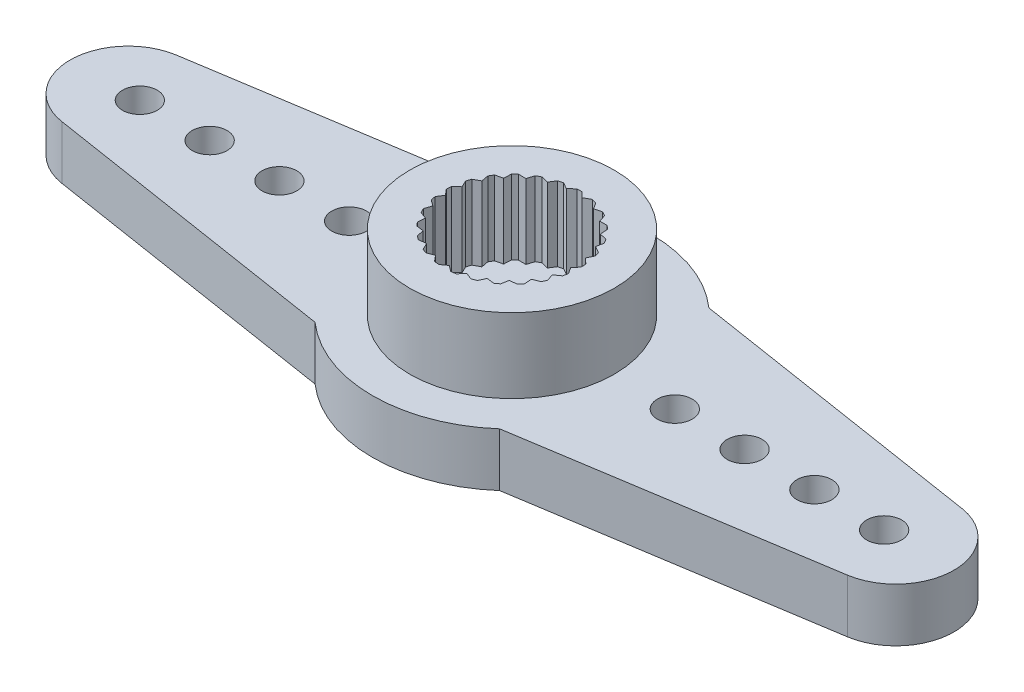
SolidWorks part; units mm, degrees
material "ABS"
ref_plane "Front Plane" through (0, 0, 0) normal (0, 0, 1) x (1, 0, 0)
ref_plane "Top Plane" through (0, 0, 0) normal (0, 1, 0) x (1, 0, 0)
ref_plane "Right Plane" through (0, 0, 0) normal (1, 0, 0) x (0, 0, -1)
sketch "Sketch2" plane through (0, 0, 0) normal (0, 1, 0) x (1, 0, 0)
  circle A0 centre (0, 0) radius 6
  circle A1 centre (0, 0) radius 1.5
  dimension "D1" = 12
  dimension "D2" = 3
extrude "Boss-Extrude1" add sketch "Sketch2" along normal mid plane 2.3
sketch "Sketch3" plane through (0, 1.15, 0) normal (0, 1, 0) x (1, 0, 0)
  line L0 (0, 0) -> (0, 2.9) construction
  line L3 (0, 0) -> (0.376, 2.9763) construction
  line L52 (0.1074, 2.898) -> (0.3384, 2.6787)
  line L53 (-0.1074, 2.898) -> (-0.3384, 2.6787)
  line L54 (0.8248, 2.7802) -> (0.9939, 2.5104)
  line L55 (0.6167, 2.8337) -> (0.3384, 2.6787)
  line L56 (1.4903, 2.4878) -> (1.587, 2.1843)
  line L57 (1.302, 2.5913) -> (0.9939, 2.5104)
  line L58 (2.0621, 2.039) -> (2.0804, 1.721)
  line L59 (1.9055, 2.1861) -> (1.587, 2.1843)
  line L60 (2.5044, 1.4621) -> (2.443, 1.1496)
  line L61 (2.3893, 1.6435) -> (2.0804, 1.721)
  line L62 (2.7894, 0.7934) -> (2.6522, 0.5059)
  line L63 (2.723, 0.9977) -> (2.443, 1.1496)
  line L64 (2.899, 0.0748) -> (2.6947, -0.1695)
  line L65 (2.8855, 0.2892) -> (2.6522, 0.5059)
  line L66 (2.8265, -0.6486) -> (2.5679, -0.8343)
  line L67 (2.8668, -0.4375) -> (2.6947, -0.1695)
  line L68 (2.5765, -1.3311) -> (2.2797, -1.4467)
  line L69 (2.6679, -1.1367) -> (2.5679, -0.8343)
  line L70 (2.1645, -1.93) -> (1.8483, -1.9682)
  line L71 (2.3014, -1.7645) -> (2.2797, -1.4467)
  line L72 (1.6165, -2.4077) -> (1.3007, -2.366)
  line L73 (1.7903, -2.2814) -> (1.8483, -1.9682)
  line L74 (0.967, -2.734) -> (0.6715, -2.6152)
  line L75 (1.1667, -2.655) -> (1.3007, -2.366)
  line L76 (0.2566, -2.8886) -> (0, -2.7)
  line L77 (0.4698, -2.8617) -> (0.6715, -2.6152)
  line L78 (-0.4698, -2.8617) -> (-0.6715, -2.6152)
  line L79 (-0.2566, -2.8886) -> (0, -2.7)
  line L80 (-1.1667, -2.655) -> (-1.3007, -2.366)
  line L81 (-0.967, -2.734) -> (-0.6715, -2.6152)
  line L82 (-1.7903, -2.2814) -> (-1.8483, -1.9682)
  line L83 (-1.6165, -2.4077) -> (-1.3007, -2.366)
  line L84 (-2.3014, -1.7645) -> (-2.2797, -1.4467)
  line L85 (-2.1645, -1.93) -> (-1.8483, -1.9682)
  line L86 (-2.6679, -1.1367) -> (-2.5679, -0.8343)
  line L87 (-2.5765, -1.3311) -> (-2.2797, -1.4467)
  line L88 (-2.8668, -0.4375) -> (-2.6947, -0.1695)
  line L89 (-2.8265, -0.6486) -> (-2.5679, -0.8343)
  line L90 (-2.8855, 0.2892) -> (-2.6522, 0.5059)
  line L91 (-2.899, 0.0748) -> (-2.6947, -0.1695)
  line L92 (-2.723, 0.9977) -> (-2.443, 1.1496)
  line L93 (-2.7894, 0.7934) -> (-2.6522, 0.5059)
  line L94 (-2.3893, 1.6435) -> (-2.0804, 1.721)
  line L95 (-2.5044, 1.4621) -> (-2.443, 1.1496)
  line L96 (-1.9055, 2.1861) -> (-1.587, 2.1843)
  line L97 (-2.0621, 2.039) -> (-2.0804, 1.721)
  line L98 (-1.302, 2.5913) -> (-0.9939, 2.5104)
  line L99 (-1.4903, 2.4878) -> (-1.587, 2.1843)
  line L100 (-0.6167, 2.8337) -> (-0.3384, 2.6787)
  line L101 (-0.8248, 2.7802) -> (-0.9939, 2.5104)
  line L102 (-2.533, 1.6075) -> (-2.3893, 1.6435) construction
  line L103 (-2.533, 1.6075) -> (-2.5044, 1.4621) construction
  line L104 (-2.8532, 0.9271) -> (-2.723, 0.9977) construction
  line L105 (-2.8532, 0.9271) -> (-2.7894, 0.7934) construction
  line L106 (-2.9941, 0.1884) -> (-2.8855, 0.2892) construction
  line L107 (-2.9941, 0.1884) -> (-2.899, 0.0748) construction
  line L108 (-2.9469, -0.5621) -> (-2.8668, -0.4375) construction
  line L109 (-2.9469, -0.5621) -> (-2.8265, -0.6486) construction
  line L110 (0, 3) -> (0.1074, 2.898) construction
  line L111 (0, 2.9) -> (0, 3) construction
  line L112 (0, 3) -> (-0.1074, 2.898) construction
  line L113 (-0.7461, 2.9057) -> (-0.6167, 2.8337) construction
  line L114 (-0.7461, 2.9057) -> (-0.8248, 2.7802) construction
  line L115 (-1.4453, 2.6289) -> (-1.302, 2.5913) construction
  line L116 (-1.4453, 2.6289) -> (-1.4903, 2.4878) construction
  line L117 (-2.0536, 2.1869) -> (-1.9055, 2.1861) construction
  line L118 (-2.0536, 2.1869) -> (-2.0621, 2.039) construction
  line L119 (-2.7145, -1.2773) -> (-2.6679, -1.1367) construction
  line L120 (-2.7145, -1.2773) -> (-2.5765, -1.3311) construction
  line L121 (-2.3115, -1.9123) -> (-2.3014, -1.7645) construction
  line L122 (-2.3115, -1.9123) -> (-2.1645, -1.93) construction
  line L123 (-1.7634, -2.4271) -> (-1.7903, -2.2814) construction
  line L124 (-1.7634, -2.4271) -> (-1.6165, -2.4077) construction
  line L125 (-1.1044, -2.7893) -> (-1.1667, -2.655) construction
  line L126 (-1.1044, -2.7893) -> (-0.967, -2.734) construction
  line L127 (-0.376, -2.9763) -> (-0.4698, -2.8617) construction
  line L128 (-0.376, -2.9763) -> (-0.2566, -2.8886) construction
  line L129 (0.376, -2.9763) -> (0.2566, -2.8886) construction
  line L130 (0.376, -2.9763) -> (0.4698, -2.8617) construction
  line L131 (1.1044, -2.7893) -> (0.967, -2.734) construction
  line L132 (1.1044, -2.7893) -> (1.1667, -2.655) construction
  line L133 (1.7634, -2.4271) -> (1.6165, -2.4077) construction
  line L134 (1.7634, -2.4271) -> (1.7903, -2.2814) construction
  line L135 (2.3115, -1.9123) -> (2.3014, -1.7645) construction
  line L136 (2.3115, -1.9123) -> (2.1645, -1.93) construction
  line L137 (2.7145, -1.2773) -> (2.6679, -1.1367) construction
  line L138 (2.7145, -1.2773) -> (2.5765, -1.3311) construction
  line L139 (2.9469, -0.5621) -> (2.8668, -0.4375) construction
  line L140 (2.9469, -0.5621) -> (2.8265, -0.6486) construction
  line L141 (2.9941, 0.1884) -> (2.8855, 0.2892) construction
  line L142 (2.9941, 0.1884) -> (2.899, 0.0748) construction
  line L143 (2.8532, 0.9271) -> (2.723, 0.9977) construction
  line L144 (2.8532, 0.9271) -> (2.7894, 0.7934) construction
  line L145 (2.533, 1.6075) -> (2.3893, 1.6435) construction
  line L146 (2.533, 1.6075) -> (2.5044, 1.4621) construction
  line L147 (2.0536, 2.1869) -> (1.9055, 2.1861) construction
  line L148 (2.0536, 2.1869) -> (2.0621, 2.039) construction
  line L149 (1.4453, 2.6289) -> (1.302, 2.5913) construction
  line L150 (1.4453, 2.6289) -> (1.4903, 2.4878) construction
  line L151 (0.7461, 2.9057) -> (0.6167, 2.8337) construction
  line L152 (0.7461, 2.9057) -> (0.8248, 2.7802) construction
  circle A0 centre (0, 0) radius 4.4
  circle A1 centre (0, 0) radius 3 construction
  circle A2 centre (0, 0) radius 2.7 construction
  arc A3 (-0.6167, 2.8337) -> (-0.8248, 2.7802) centre (0, 0) ccw
  arc A4 (-0.1074, 2.898) -> (-0.6167, 2.8337) centre (0, 0) ccw construction
  arc A5 (-0.8248, 2.7802) -> (-1.302, 2.5913) centre (0, 0) ccw construction
  arc A6 (-1.302, 2.5913) -> (-1.4903, 2.4878) centre (0, 0) ccw
  arc A7 (-1.4903, 2.4878) -> (-1.9055, 2.1861) centre (0, 0) ccw construction
  arc A8 (-1.9055, 2.1861) -> (-2.0621, 2.039) centre (0, 0) ccw
  arc A9 (-2.0621, 2.039) -> (-2.3893, 1.6435) centre (0, 0) ccw construction
  arc A10 (-2.3893, 1.6435) -> (-2.5044, 1.4621) centre (0, 0) ccw
  arc A11 (-2.5044, 1.4621) -> (-2.723, 0.9977) centre (0, 0) ccw construction
  arc A12 (-2.723, 0.9977) -> (-2.7894, 0.7934) centre (0, 0) ccw
  arc A13 (-2.7894, 0.7934) -> (-2.8855, 0.2892) centre (0, 0) ccw construction
  arc A14 (-2.8855, 0.2892) -> (-2.899, 0.0748) centre (0, 0) ccw
  arc A15 (-2.899, 0.0748) -> (-2.8668, -0.4375) centre (0, 0) ccw construction
  arc A16 (-2.8668, -0.4375) -> (-2.8265, -0.6486) centre (0, 0) ccw
  arc A17 (-2.8265, -0.6486) -> (-2.6679, -1.1367) centre (0, 0) ccw construction
  arc A18 (-2.6679, -1.1367) -> (-2.5765, -1.3311) centre (0, 0) ccw
  arc A19 (-2.5765, -1.3311) -> (-2.3014, -1.7645) centre (0, 0) ccw construction
  arc A20 (-2.3014, -1.7645) -> (-2.1645, -1.93) centre (0, 0) ccw
  arc A21 (-2.1645, -1.93) -> (-1.7903, -2.2814) centre (0, 0) ccw construction
  arc A22 (-1.7903, -2.2814) -> (-1.6165, -2.4077) centre (0, 0) ccw
  arc A23 (-1.6165, -2.4077) -> (-1.1667, -2.655) centre (0, 0) ccw construction
  arc A24 (-1.1667, -2.655) -> (-0.967, -2.734) centre (0, 0) ccw
  arc A25 (-0.967, -2.734) -> (-0.4698, -2.8617) centre (0, 0) ccw construction
  arc A26 (-0.4698, -2.8617) -> (-0.2566, -2.8886) centre (0, 0) ccw
  arc A27 (-0.2566, -2.8886) -> (0.2566, -2.8886) centre (0, 0) ccw construction
  arc A28 (0.2566, -2.8886) -> (0.4698, -2.8617) centre (0, 0) ccw
  arc A29 (0.4698, -2.8617) -> (0.967, -2.734) centre (0, 0) ccw construction
  arc A30 (0.967, -2.734) -> (1.1667, -2.655) centre (0, 0) ccw
  arc A31 (1.1667, -2.655) -> (1.6165, -2.4077) centre (0, 0) ccw construction
  arc A32 (1.6165, -2.4077) -> (1.7903, -2.2814) centre (0, 0) ccw
  arc A33 (1.7903, -2.2814) -> (2.1645, -1.93) centre (0, 0) ccw construction
  arc A34 (2.1645, -1.93) -> (2.3014, -1.7645) centre (0, 0) ccw
  arc A35 (2.3014, -1.7645) -> (2.5765, -1.3311) centre (0, 0) ccw construction
  arc A36 (2.5765, -1.3311) -> (2.6679, -1.1367) centre (0, 0) ccw
  arc A37 (2.6679, -1.1367) -> (2.8265, -0.6486) centre (0, 0) ccw construction
  arc A38 (2.8265, -0.6486) -> (2.8668, -0.4375) centre (0, 0) ccw
  arc A39 (2.8668, -0.4375) -> (2.899, 0.0748) centre (0, 0) ccw construction
  arc A40 (2.899, 0.0748) -> (2.8855, 0.2892) centre (0, 0) ccw
  arc A41 (2.8855, 0.2892) -> (2.7894, 0.7934) centre (0, 0) ccw construction
  arc A42 (2.7894, 0.7934) -> (2.723, 0.9977) centre (0, 0) ccw
  arc A43 (2.723, 0.9977) -> (2.5044, 1.4621) centre (0, 0) ccw construction
  arc A44 (2.5044, 1.4621) -> (2.3893, 1.6435) centre (0, 0) ccw
  arc A45 (2.3893, 1.6435) -> (2.0621, 2.039) centre (0, 0) ccw construction
  arc A46 (2.0621, 2.039) -> (1.9055, 2.1861) centre (0, 0) ccw
  arc A47 (1.9055, 2.1861) -> (1.4903, 2.4878) centre (0, 0) ccw construction
  arc A48 (1.4903, 2.4878) -> (1.302, 2.5913) centre (0, 0) ccw
  arc A49 (1.302, 2.5913) -> (0.8248, 2.7802) centre (0, 0) ccw construction
  arc A50 (0.8248, 2.7802) -> (0.6167, 2.8337) centre (0, 0) ccw
  arc A51 (0.3635, 2.8771) -> (0.1074, 2.898) centre (0, 0) ccw construction
  arc A52 (0.1074, 2.898) -> (-0.1074, 2.898) centre (0, 0) ccw
  arc A53 (0.6167, 2.8337) -> (0.3635, 2.8771) centre (0, 0) ccw construction
  point P84 (0, 0)
  dimension "D1" = 8.8
  dimension "D2" = 5.4
  dimension "D3" = 6
  dimension "D6" = 5.8
  dimension "D4" = 7.2
  dimension "D5" = 25
extrude "Boss-Extrude2" add sketch "Sketch3" along normal blind 3.2
sketch "Sketch4" plane through (0, 0, 0) normal (0, 1, 0) x (1, 0, 0)
  line L0 (0, 0) -> (16, 0) construction
  line L1 (3.9686, 4.5) -> (16.8881, 2.4697)
  line L2 (3.9686, -4.5) -> (16.8881, -2.4697)
  line L3 (16, 0) -> (13, 0) construction
  circle A0 centre (0, 0) radius 6 construction
  arc A1 (3.9686, -4.5) -> (3.9686, 4.5) centre (0, 0) ccw
  arc A2 (16.8881, 2.4697) -> (16.8881, -2.4697) centre (16.5, 0) cw
  circle A3 centre (16, 0) radius 0.75
  circle A4 centre (13, 0) radius 0.75
  circle A5 centre (10, 0) radius 0.75
  circle A6 centre (7, 0) radius 0.75
  dimension "D3" = 2.5
  dimension "D5" = 1.5
  dimension "D2" = 9
  dimension "D7" = 3
  dimension "D4" = 0.5
extrude "Boss-Extrude3" add sketch "Sketch4" along normal mid plane 2.3
pattern_circular "CirPattern1" count 2 over 360 about axis through (0, 0, 0) along (0, 1, 0) of "Boss-Extrude3"
sketch "Sketch5" [suppressed] plane through (0, 0, 0) normal (0, 1, 0) x (1, 0, 0)
  line L0 (3, 7) -> (-3, 7) construction
  circle A0 centre (0, 0) radius 10
  circle A1 centre (0, 7) radius 0.75
  circle A2 centre (-3, 7) radius 0.75
  circle A3 centre (3, 7) radius 0.75
  circle A4 centre (7, 3) radius 0.75
  circle A5 centre (7, 0) radius 0.75
  circle A6 centre (7, -3) radius 0.75
  circle A7 centre (3, -7) radius 0.75
  circle A8 centre (0, -7) radius 0.75
  circle A9 centre (-3, -7) radius 0.75
  circle A10 centre (-7, -3) radius 0.75
  circle A11 centre (-7, 0) radius 0.75
  circle A12 centre (-7, 3) radius 0.75
  circle A13 centre (0, 0) radius 1.5 construction
  circle A14 centre (0, 0) radius 1.5
  point P8 (0, 7)
  point P31 (0, 0)
  dimension "D1" = 1.5
  dimension "D3" = 2.25
  dimension "D4" = 6
  dimension "D2" = 7
  dimension "D5" = 4
extrude "Boss-Extrude4" [suppressed] add sketch "Sketch5" along normal mid plane 2.3
equation "\"N_hole\"= 4"
equation "\"N_horn\"= 2"
equation "\"D6@Sketch4\"=\"N_hole\""
equation "\"D1@CirPattern1\"=\"N_horn\""
equation "\"D1@Sketch4\"=(\"N_hole\" - 1) *3 +7"
